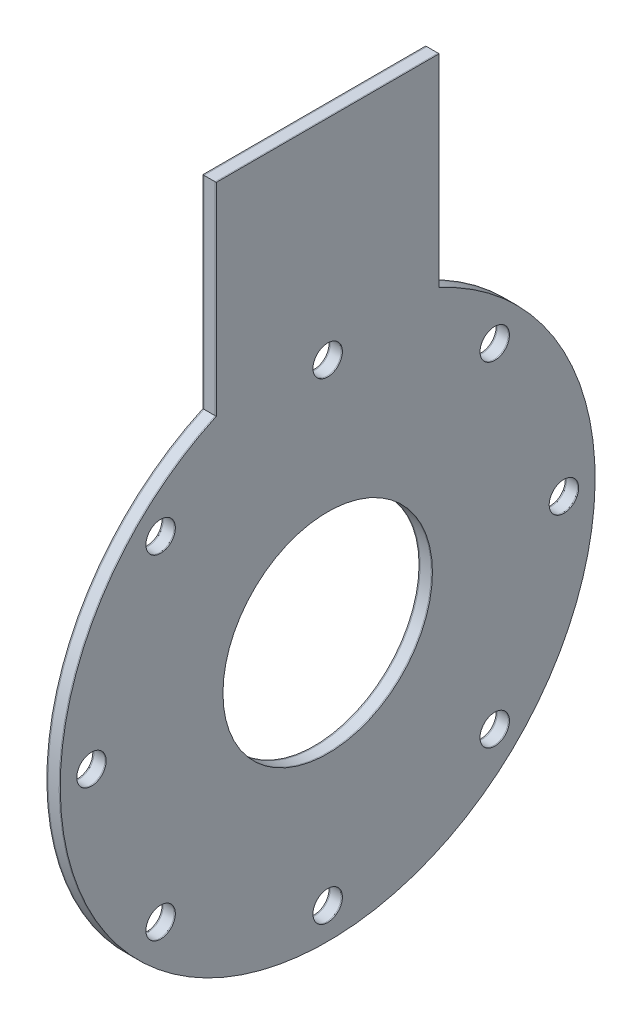
SolidWorks part; units mm, degrees
ref_plane "Front Plane" through (0, 0, 0) normal (0, 0, 1) x (1, 0, 0)
ref_plane "Top Plane" through (0, 0, 0) normal (0, 1, 0) x (1, 0, 0)
ref_plane "Right Plane" through (0, 0, 0) normal (1, 0, 0) x (0, 0, -1)
sketch "Sketch1" plane through (0, 0, 0) normal (1, 0, 0) x (0, 0, -1)
  line L0 (-25, 100) -> (25, 100)
  line L1 (-25, 100) -> (-25, 54.5436)
  line L2 (25, 100) -> (25, 54.5436)
  circle A0 centre (0, 0) radius 60
  circle A1 centre (0, 0) radius 23.5
  point P7 (0, 100)
  dimension "D1" = 120
  dimension "D2" = 47
  dimension "D3" = 40
  dimension "D4" = 50
extrude "Boss-Extrude1" add sketch "Sketch1" along normal blind 0.25 contours A0 L2 L0 L1 | A0 A1
sketch "Sketch4" plane through (0, 0, 0) normal (-1, 0, 0) x (0, 0, 1)
  line L3 (25, 54.5436) -> (25, 100)
  line L4 (25, 100) -> (-25, 100)
  line L5 (-25, 100) -> (-25, 54.5436)
  line L6 (25, 54.5436) -> (25, 100)
  line L7 (25, 100) -> (-25, 100)
  line L8 (-25, 100) -> (-25, 54.5436)
  circle A0 centre (0, 0) radius 23.5 construction
  arc A1 (-25, 54.5436) -> (25, 54.5436) centre (0, 0) ccw
  arc A2 (-25, 54.5436) -> (25, 54.5436) centre (0, 0) ccw
  circle A3 centre (0, 0) radius 23.5
  dimension "D1" = 0
extrude "Boss-Extrude4" add sketch "Sketch4" along normal blind 2.5 separate body
sketch "Sketch5" plane through (-2.5, 0, 0) normal (-1, 0, 0) x (0, 0, 1)
  line L3 (25, 54.5436) -> (25, 100)
  line L4 (25, 100) -> (-25, 100)
  line L5 (-25, 100) -> (-25, 54.5436)
  line L6 (25, 54.5436) -> (25, 100)
  line L7 (25, 100) -> (-25, 100)
  line L8 (-25, 100) -> (-25, 54.5436)
  circle A0 centre (0, 0) radius 23.5 construction
  arc A1 (-25, 54.5436) -> (25, 54.5436) centre (0, 0) ccw
  arc A2 (-25, 54.5436) -> (25, 54.5436) centre (0, 0) ccw
  circle A3 centre (0, 0) radius 23.5
  dimension "D1" = 0
extrude "Boss-Extrude5" add sketch "Sketch5" along normal blind 0.25 separate body contours A2 L6 L7 L8
sketch "Sketch9" plane through (0.25, 0, 0) normal (1, 0, 0) x (0, 0, -1)
  circle A0 centre (0, 0) radius 53
  point P3 (53, 0)
  point P6 (37.4767, -37.4767)
  point P7 (0, -53)
  point P8 (-37.4767, -37.4767)
  point P9 (-53, 0)
  point P10 (-37.4767, 37.4767)
  point P11 (0, 53)
  point P12 (37.4767, 37.4767)
  dimension "D1" = 106
  dimension "D2" = 8
hole_wizard "M6 Clearance Hole1" positions "Sketch9" profile "Sketch10" hole size "M6" standard "ISO" end condition through all
sketch "Sketch10" plane through (0.25, 37.4767, -37.4767) normal (0, 1, 0) x (0, 0, -1)
  line L0 (0, 0) -> (0, 3)
  line L1 (0, 3) -> (3.3, 3)
  line L2 (3.3, 3) -> (3.3, 0)
  line L5 (3.3, 0) -> (0, 0)
  line L11 (0, -6.35) -> (0, 107.95) construction
  dimension "Thru Hole Dia." = 6.6
  dimension "Thru Hole Depth" = 3
